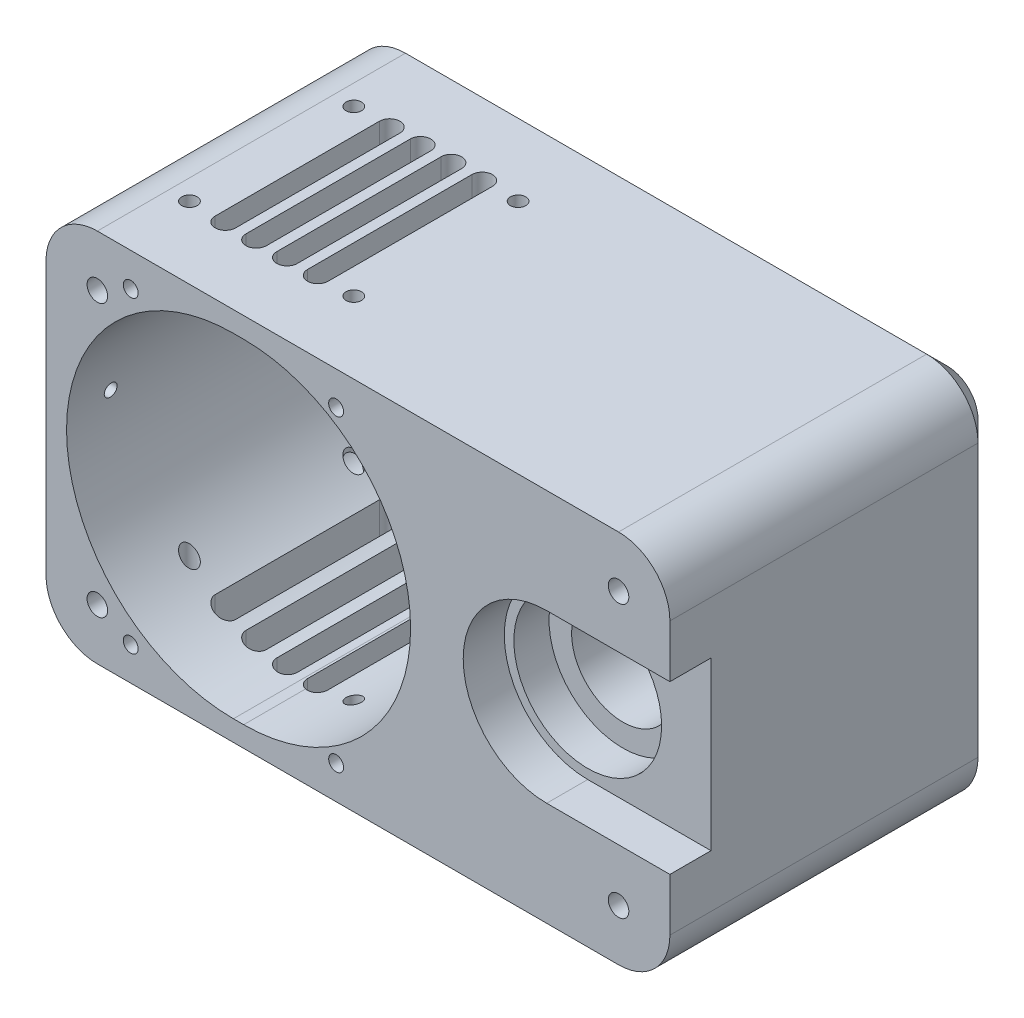
SolidWorks part; units mm, degrees
ref_plane "Front Plane" through (0, 0, 0) normal (0, 0, 1) x (1, 0, 0)
ref_plane "Top Plane" through (0, 0, 0) normal (0, 1, 0) x (1, 0, 0)
ref_plane "Right Plane" through (0, 0, 0) normal (1, 0, 0) x (0, 0, -1)
sketch "Sketch1" plane through (0, 0, 0) normal (0, 0, 1) x (1, 0, 0)
  line L1 (0, 36.5) -> (85, 36.5)
  line L2 (0, 36.5) -> (0, -36.5)
  line L3 (0, -36.5) -> (85, -36.5)
  line L4 (85, 36.5) -> (85, -36.5)
  line L5 (0, 36.5) -> (-36.5, 36.5)
  line L6 (0, 36.5) -> (0, -36.5)
  line L7 (0, -36.5) -> (-36.5, -36.5)
  line L8 (-36.5, 36.5) -> (-36.5, -36.5)
  circle A0 centre (0, 0) radius 36.5
  dimension "D1" = 73
  dimension "D2" = 85
  dimension "D3" = 36.5
extrude "Boss-Extrude1" add sketch "Sketch1" along normal blind 64 contours L2 A0 | L2 A0 | A0 L3 L4 L1 | L6 L5 L8 L7
sketch "Sketch2" plane through (0, 0, 64) normal (0, 0, 1) x (1, 0, 0)
  circle A0 centre (0, 0) radius 32.5
  dimension "D1" = 65
extrude "Cut-Extrude1" cut sketch "Sketch2" against normal offset from surface (60 mm away) 4 up to face at (24.25, 0, 0)
sketch "Sketch3" plane through (0, 0, 0) normal (0, 0, -1) x (-1, 0, 0)
  circle A0 centre (0, 0) radius 10
  dimension "D1" = 20
extrude "Cut-Extrude2" cut sketch "Sketch3" against normal blind 4
sketch "Sketch11" plane through (0, 0, 4) normal (0, 0, 1) x (1, 0, 0)
  line L0 (0, 0) -> (2, 0) construction
  line L1 (0, 32.5) -> (2, 32.5)
  line L2 (0, -32.5) -> (2, -32.5)
  arc A0 (0, 32.5) -> (0, -32.5) centre (0, 0) ccw
  arc A1 (2, -32.5) -> (2, 32.5) centre (2, 0) ccw
  point P3 (1, 0)
  dimension "D1" = 32.5
  dimension "D2" = 2
extrude "Cut-Extrude10" cut sketch "Sketch11" along normal through all
chamfer "Chamfer1" distance 4 angle 45 4 edges at (-32.5, 0, 4) (34.5, 0, 4) (1, -32.5, 4) (1, 32.5, 4)
fillet "Fillet1" radius 10 4 edges at (85, -36.5, 32) (85, 36.5, 32) (-36.5, -36.5, 32) (-36.5, 36.5, 32)
sketch "Sketch4" plane through (0, 0, 0) normal (0, 0, -1) x (-1, 0, 0)
  circle A0 centre (-61, 0) radius 14.3875
  circle A1 centre (0, 0) radius 10 construction
  dimension "D1" = 61
  dimension "D2" = 28.775
extrude "Cut-Extrude3" cut sketch "Sketch4" against normal blind 6.86
sketch "Sketch5" plane through (0, 0, 6.86) normal (0, 0, -1) x (-1, 0, 0)
  circle A1 centre (-61, 0) radius 10
  dimension "D2" = 20
extrude "Cut-Extrude4" cut sketch "Sketch5" against normal through all
sketch "Sketch6" plane through (0, 0, 64) normal (0, 0, 1) x (1, 0, 0)
  circle A0 centre (61, 0) radius 16.25
  dimension "D1" = 32.5
extrude "Cut-Extrude5" cut sketch "Sketch6" against normal blind 8
sketch "Sketch7" plane through (0, 0, 56) normal (0, 0, 1) x (1, 0, 0)
  circle A0 centre (61, 0) radius 14.3875
  dimension "D1" = 28.775
extrude "Cut-Extrude6" cut sketch "Sketch7" against normal blind 6.85
chamfer "Chamfer5" distance 4 angle 45 8 edges at (24.25, -36.5, 0) (-33.5711, -33.5711, 0) (82.0711, -33.5711, 0) (-36.5, 0, 0) (85, 0, 0) (-33.5711, 33.5711, 0) (82.0711, 33.5711, 0) (24.25, 36.5, 0)
sketch "Sketch9" plane through (0, 0, 0) normal (0, 0, -1) x (-1, 0, 0)
  line L0 (0, 0) -> (24.8728, 25.111) construction
  line L1 (24.8728, 25.111) -> (-27.9579, -28.2257) construction
  line L2 (-27.9579, -28.2257) -> (0, 0) construction
  line L3 (0, 0) -> (27.5081, -27.2471) construction
  line L4 (27.5081, -27.2471) -> (-23.1956, 22.9755) construction
  circle A0 centre (15.6228, 15.7724) radius 2
  circle A1 centre (10.6967, 10.7991) radius 2
  circle A2 centre (10.7991, -10.6967) radius 2
  circle A3 centre (15.7724, -15.6228) radius 2
  circle A4 centre (-10.6967, -10.7991) radius 2
  circle A5 centre (-15.6228, -15.7724) radius 2
  circle A6 centre (-10.7991, 10.6967) radius 2
  circle A7 centre (-15.7724, 15.6228) radius 2
  point P20 (0, 0)
  dimension "D2" = 22.2
  dimension "D3" = 4
  dimension "D4" = 4
  dimension "D1" = 15.2
  dimension "D5" = 4
extrude "Cut-Extrude8" cut sketch "Sketch9" against normal blind 4
sketch "Sketch10" plane through (0, 0, 0) normal (0, 0, -1) x (-1, 0, 0)
  line L0 (15.6228, 15.7724) -> (13.6228, 15.7724) construction
  line L1 (15.6228, 13.7724) -> (13.6228, 13.7724)
  line L2 (15.6228, 17.7724) -> (13.6228, 17.7724)
  line L3 (10.6967, 10.7991) -> (8.6967, 10.7991) construction
  line L4 (10.6967, 8.7991) -> (8.6967, 8.7991)
  line L5 (10.6967, 12.7991) -> (8.6967, 12.7991)
  line L6 (15.7724, -15.6228) -> (13.7724, -15.6228) construction
  line L9 (15.7724, -17.6228) -> (13.7724, -17.6228)
  line L12 (15.7724, -13.6228) -> (13.7724, -13.6228)
  line L15 (10.7991, -10.6967) -> (8.7991, -10.6967) construction
  line L18 (-10.6967, -10.7991) -> (-12.6967, -10.7991) construction
  line L19 (-10.6967, -12.7991) -> (-12.6967, -12.7991)
  line L20 (-10.6967, -8.7991) -> (-12.6967, -8.7991)
  line L21 (-15.6228, -15.7724) -> (-17.6228, -15.7724) construction
  line L22 (-15.6228, -17.7724) -> (-17.6228, -17.7724)
  line L23 (-15.6228, -13.7724) -> (-17.6228, -13.7724)
  line L24 (0, 0) -> (-2, 0) construction
  line L25 (0, -10) -> (-2, -10)
  line L26 (0, 10) -> (-2, 10)
  line L27 (10.7991, -12.6967) -> (8.7991, -12.6967)
  line L28 (10.7991, -8.6967) -> (8.7991, -8.6967)
  line L29 (-10.7991, 10.6967) -> (-12.7991, 10.6967) construction
  line L30 (-10.7991, 8.6967) -> (-12.7991, 8.6967)
  line L31 (-10.7991, 12.6967) -> (-12.7991, 12.6967)
  line L32 (-15.7724, 15.6228) -> (-17.7724, 15.6228) construction
  line L33 (-15.7724, 13.6228) -> (-17.7724, 13.6228)
  line L34 (-15.7724, 17.6228) -> (-17.7724, 17.6228)
  arc A0 (15.6228, 13.7724) -> (15.6228, 17.7724) centre (15.6228, 15.7724) ccw
  arc A1 (13.6228, 17.7724) -> (13.6228, 13.7724) centre (13.6228, 15.7724) ccw
  arc A2 (10.6967, 8.7991) -> (10.6967, 12.7991) centre (10.6967, 10.7991) ccw
  arc A3 (8.6967, 12.7991) -> (8.6967, 8.7991) centre (8.6967, 10.7991) ccw
  arc A12 (-10.6967, -12.7991) -> (-10.6967, -8.7991) centre (-10.6967, -10.7991) ccw
  arc A13 (-12.6967, -8.7991) -> (-12.6967, -12.7991) centre (-12.6967, -10.7991) ccw
  arc A14 (-15.6228, -17.7724) -> (-15.6228, -13.7724) centre (-15.6228, -15.7724) ccw
  arc A15 (-17.6228, -13.7724) -> (-17.6228, -17.7724) centre (-17.6228, -15.7724) ccw
  arc A16 (0, -10) -> (0, 10) centre (0, 0) ccw
  arc A17 (-2, 10) -> (-2, -10) centre (-2, 0) ccw
  arc A23 (15.7724, -17.6228) -> (15.7724, -13.6228) centre (15.7724, -15.6228) ccw
  arc A24 (13.7724, -13.6228) -> (13.7724, -17.6228) centre (13.7724, -15.6228) ccw
  arc A25 (10.7991, -12.6967) -> (10.7991, -8.6967) centre (10.7991, -10.6967) ccw
  arc A26 (8.7991, -8.6967) -> (8.7991, -12.6967) centre (8.7991, -10.6967) ccw
  arc A27 (-10.7991, 8.6967) -> (-10.7991, 12.6967) centre (-10.7991, 10.6967) ccw
  arc A28 (-12.7991, 12.6967) -> (-12.7991, 8.6967) centre (-12.7991, 10.6967) ccw
  arc A29 (-15.7724, 13.6228) -> (-15.7724, 17.6228) centre (-15.7724, 15.6228) ccw
  arc A30 (-17.7724, 17.6228) -> (-17.7724, 13.6228) centre (-17.7724, 15.6228) ccw
  point P3 (14.6228, 15.7724)
  point P8 (9.6967, 10.7991)
  point P16 (21.2, 0)
  point P21 (14.7724, -15.6228)
  point P25 (14.2, 0)
  point P27 (9.7991, -10.6967)
  point P33 (-16.2, 0)
  point P37 (-11.7991, 10.6967)
  point P41 (-23.2, 0)
  point P46 (-16.7724, 15.6228)
  point P49 (-11.6967, -10.7991)
  point P57 (-16.6228, -15.7724)
  point P67 (-1, 0)
  dimension "D9" = 2
  dimension "D10" = 2
  dimension "D11" = 2
  dimension "D12" = 2
  dimension "D13" = 2
  dimension "D14" = 2
  dimension "D15" = 2
  dimension "D16" = 2
  dimension "D17" = 10
  dimension "D19" = 2
  dimension "D1" = 2
  dimension "D2" = 2
  dimension "D3" = 2
  dimension "D4" = 2
  dimension "D5" = 2
  dimension "D6" = 2
  dimension "D7" = 2
  dimension "D8" = 2
  dimension "D18" = 2
extrude "Cut-Extrude9" cut sketch "Sketch10" against normal through all
sketch "Sketch12" plane through (0, 0, 64) normal (0, 0, 1) x (1, 0, 0)
  circle A0 centre (-26.5, -26.5) radius 2
  circle A1 centre (-26.5, 26.5) radius 2
  circle A2 centre (75, 26.5) radius 2
  circle A3 centre (75, -26.5) radius 2
  dimension "D1" = 4
  dimension "D2" = 4
  dimension "D3" = 4
  dimension "D4" = 4
extrude "Cut-Extrude11" cut sketch "Sketch12" against normal through all
sketch "Sketch13" plane through (0, 0, 0) normal (0, 0, -1) x (-1, 0, 0)
  circle A0 centre (-75, 26.5) radius 4.5
  circle A1 centre (-75, -26.5) radius 4.5
  circle A2 centre (26.5, -26.5) radius 4.5
  circle A3 centre (26.5, 26.5) radius 4.5
  dimension "D1" = 9
  dimension "D2" = 9
  dimension "D3" = 9
  dimension "D4" = 9
extrude "Cut-Extrude12" cut sketch "Sketch13" against normal blind 40
sketch "Sketch16" plane through (-36.5, 0, 0) normal (-1, 0, 0) x (0, 0, 1)
  line L0 (9, 7.5) -> (9, -7.5) construction
  line L1 (13, 7.5) -> (13, -7.5)
  line L2 (5, 7.5) -> (5, -7.5)
  line L3 (4, 26.5) -> (4, -26.5) construction
  arc A0 (13, 7.5) -> (5, 7.5) centre (9, 7.5) ccw
  arc A1 (5, -7.5) -> (13, -7.5) centre (9, -7.5) ccw
  point P2 (9, 0)
  dimension "D2" = 4
  dimension "D1" = 15
  dimension "D3" = 1
extrude "Cut-Extrude15" cut sketch "Sketch16" against normal blind 20
sketch "Sketch17" plane through (-36.5, 0, 0) normal (-1, 0, 0) x (0, 0, 1)
  line L0 (60, -26.5) -> (60, 26.5) construction
  line L1 (64, 26.5) -> (4, 26.5) construction
  circle A0 centre (28.5, 21.5) radius 1.25
  circle A1 centre (55.5, 21.5) radius 1.25
  circle A2 centre (28.5, 2.5) radius 1.25
  circle A3 centre (55.5, 2.5) radius 1.25
  dimension "D1" = 2.5
  dimension "D2" = 2.5
  dimension "D3" = 2.5
  dimension "D4" = 2.5
  dimension "D5" = 19
  dimension "D6" = 19
  dimension "D7" = 27
  dimension "D8" = 4.5
  dimension "D9" = 5
extrude "Cut-Extrude16" cut sketch "Sketch17" against normal blind 6
sketch "Sketch19" plane through (0, -36.5, 0) normal (0, -1, 0) x (1, 0, 0)
  line L0 (75, 60) -> (-26.5, 60) construction
  line L1 (75, 4) -> (75, 64) construction
  circle A0 centre (35, 51) radius 1.25
  circle A1 centre (35, 24) radius 1.25
  circle A2 centre (16, 51) radius 1.25
  circle A3 centre (16, 24) radius 1.25
  dimension "D1" = 2.5
  dimension "D2" = 2.5
  dimension "D3" = 27
  dimension "D5" = 9
  dimension "D6" = 40
  dimension "D4" = 2
extrude "Cut-Extrude17" cut sketch "Sketch19" against normal blind 5
sketch "Sketch20" plane through (0, 0, 0) normal (0, 0, -1) x (-1, 0, 0)
  line L0 (36.5, 26.5) -> (36.5, -26.5) construction
  line L1 (-75, 36.5) -> (26.5, 36.5) construction
  line L2 (26.5, -36.5) -> (-75, -36.5) construction
  circle A0 centre (-5.5, 30.5) radius 1.7416
  circle A1 centre (-5.5, -30.5) radius 2
  dimension "D1" = 42
  dimension "D2" = 4
  dimension "D3" = 42
  dimension "D4" = 6
  dimension "D5" = 6
extrude "Cut-Extrude18" cut sketch "Sketch20" against normal blind 8
sketch "Sketch21" plane through (0, 0, 64) normal (0, 0, 1) x (1, 0, 0)
  line L1 (61, 16.25) -> (104.2877, 16.25)
  line L2 (61, 16.25) -> (61, -16.25)
  line L3 (61, -16.25) -> (104.2877, -16.25)
  line L4 (104.2877, 16.25) -> (104.2877, -16.25)
  circle A0 centre (61, 0) radius 16.25 construction
  circle A1 centre (61, 0) radius 16.25 construction
  dimension "D1" = 32.5
extrude "Cut-Extrude19" cut sketch "Sketch21" against normal up to surface (8 mm away) up to face at (75.3875, 0, 56)
sketch "Sketch22" plane through (0, 0, 64) normal (0, 0, 1) x (1, 0, 0)
  line L0 (0, 17.4602) -> (0, -19.0691) construction
  line L1 (0, -19.0691) -> (0, 0) construction
  line L2 (0, 0) -> (17.2058, 0) construction
  line L3 (17.2058, 0) -> (-14.5674, 0) construction
  circle A0 centre (-20, 30) radius 1.45
  circle A1 centre (20, 30) radius 1.45
  circle A2 centre (20, -30) radius 1.45
  circle A3 centre (-20, -30) radius 1.45
  dimension "D1" = 20
  dimension "D2" = 30
  dimension "D3" = 2.9
extrude "Cut-Extrude20" cut sketch "Sketch22" against normal blind 20
sketch "Sketch23" plane through (0, -36.5, 0) normal (0, -1, 0) x (1, 0, 0)
  line L0 (-15.5622, 50) -> (-15.5622, 18) construction
  line L1 (-13.5622, 50) -> (-13.5622, 18)
  line L2 (-17.5622, 50) -> (-17.5622, 18)
  line L3 (-26.5, 64) -> (-26.5, 4) construction
  line L4 (-9.5622, 50) -> (-9.5622, 18) construction
  line L5 (-7.5622, 50) -> (-7.5622, 18)
  line L6 (-11.5622, 50) -> (-11.5622, 18)
  line L7 (-3.5622, 50) -> (-3.5622, 18) construction
  line L8 (-1.5622, 50) -> (-1.5622, 18)
  line L9 (-5.5622, 50) -> (-5.5622, 18)
  line L10 (2.4378, 50) -> (2.4378, 18) construction
  line L11 (4.4378, 50) -> (4.4378, 18)
  line L12 (0.4378, 50) -> (0.4378, 18)
  arc A0 (-13.5622, 50) -> (-17.5622, 50) centre (-15.5622, 50) ccw
  arc A1 (-17.5622, 18) -> (-13.5622, 18) centre (-15.5622, 18) ccw
  arc A2 (-7.5622, 50) -> (-11.5622, 50) centre (-9.5622, 50) ccw
  arc A3 (-11.5622, 18) -> (-7.5622, 18) centre (-9.5622, 18) ccw
  arc A4 (-1.5622, 50) -> (-5.5622, 50) centre (-3.5622, 50) ccw
  arc A5 (-5.5622, 18) -> (-1.5622, 18) centre (-3.5622, 18) ccw
  arc A6 (4.4378, 50) -> (0.4378, 50) centre (2.4378, 50) ccw
  arc A7 (0.4378, 18) -> (4.4378, 18) centre (2.4378, 18) ccw
  point P2 (-15.5622, 34)
  point P7 (-26.5, 34)
  point P14 (-9.5622, 34)
  point P21 (-3.5622, 34)
  point P28 (2.4378, 34)
  dimension "D2" = 2
  dimension "D1" = 32
  dimension "D3" = 4
extrude "Cut-Extrude21" cut sketch "Sketch23" against normal through all
sketch "Sketch24" plane through (0, 36.5, 0) normal (0, 1, 0) x (1, 0, 0)
  line L0 (-17.5622, -34) -> (13.6803, -34) construction
  line L1 (-17.5622, -50) -> (-17.5622, -18) construction
  line L2 (-6.5622, -7.7586) -> (-6.5622, -61.0474) construction
  line L3 (-5.5622, -50) -> (-5.5622, -18) construction
  circle A0 centre (-22.5622, -18) radius 1.5
  circle A1 centre (-22.5622, -50) radius 1.5
  circle A2 centre (9.4378, -18) radius 1.5
  circle A3 centre (9.4378, -50) radius 1.5
  dimension "D1" = 3
  dimension "D2" = 16
  dimension "D4" = 1
  dimension "D5" = 16
  dimension "D3" = 2
extrude "Cut-Extrude22" cut sketch "Sketch24" against normal through all
